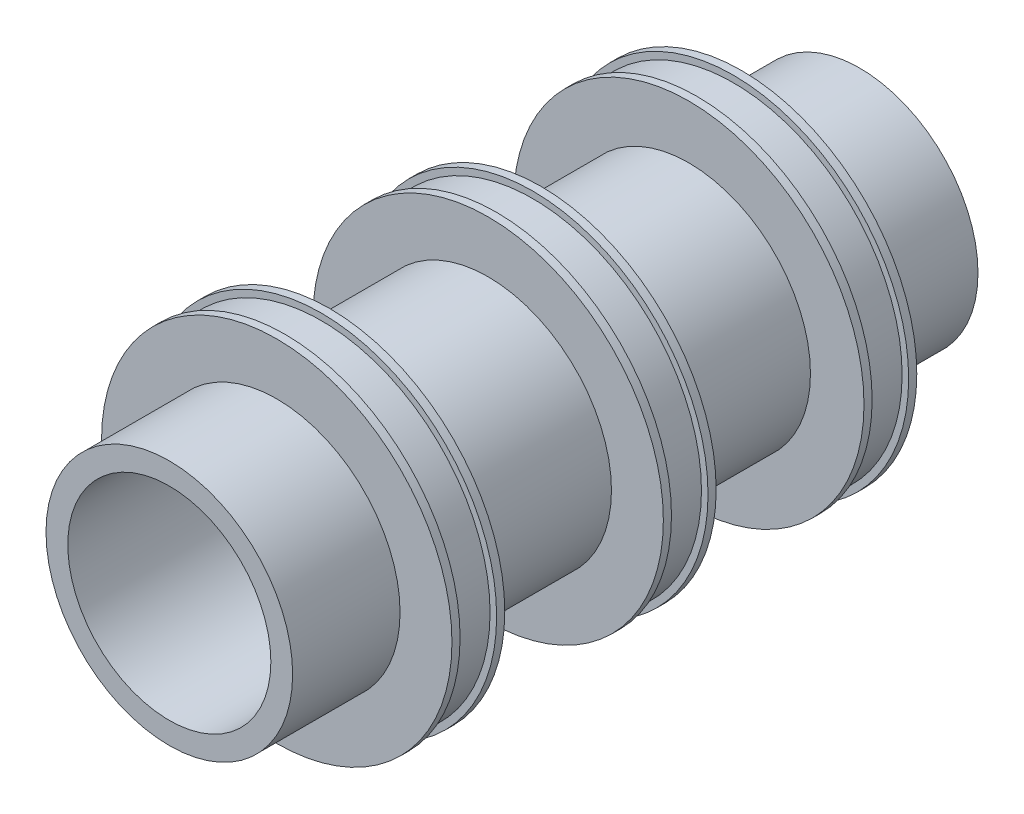
SolidWorks part; units mm, degrees
ref_plane "Front Plane" through (0, 0, 0) normal (0, 0, 1) x (1, 0, 0)
ref_plane "Top Plane" through (0, 0, 0) normal (0, 1, 0) x (1, 0, 0)
ref_plane "Right Plane" through (0, 0, 0) normal (1, 0, 0) x (0, 0, -1)
sketch "Sketch1" plane through (0, 0, 0) normal (1, 0, 0) x (0, 0, -1)
  line L0 (-119.0608, 0) -> (108.9248, 0) construction
  line L1 (-119.0608, 25) -> (108.9248, 25) construction
  line L30 (-85, 25) -> (85, 25)
  line L31 (-85, 25) -> (-85, 30.3639)
  line L32 (-85, 30.3639) -> (-58.5522, 30.3639)
  line L33 (-58.5522, 30.3639) -> (-58.5522, 43.1442)
  line L34 (-58.5522, 43.1442) -> (-56.5522, 43.1442)
  line L35 (-56.5522, 43.1442) -> (-56.5522, 41.53)
  line L36 (-56.5522, 41.53) -> (-47.5522, 41.53)
  line L37 (-47.5522, 41.53) -> (-47.5522, 43.1442)
  line L38 (-47.5522, 43.1442) -> (-45.5522, 43.1442)
  line L39 (-45.5522, 43.1442) -> (-45.5522, 30.3639)
  line L40 (-45.5522, 30.3639) -> (-6.5, 30.3639)
  line L41 (-6.5, 30.3639) -> (-6.5, 43.1442)
  line L42 (-6.5, 43.1442) -> (-4.5, 43.1442)
  line L43 (-4.5, 43.1442) -> (-4.5, 41.53)
  line L44 (-4.5, 41.53) -> (4.5, 41.53)
  line L45 (4.5, 41.53) -> (4.5, 43.1442)
  line L46 (4.5, 43.1442) -> (6.5, 43.1442)
  line L47 (6.5, 43.1442) -> (6.5, 29.9619)
  line L48 (6.5, 29.9619) -> (42.9013, 29.9619)
  line L49 (42.9013, 29.9619) -> (42.9013, 43.1442)
  line L50 (42.9013, 43.1442) -> (44.9013, 43.1442)
  line L51 (44.9013, 43.1442) -> (44.9013, 41.53)
  line L52 (44.9013, 41.53) -> (53.9013, 41.53)
  line L53 (53.9013, 41.53) -> (53.9013, 43.1442)
  line L54 (53.9013, 43.1442) -> (55.9013, 43.1442)
  line L55 (55.9013, 43.1442) -> (55.9013, 29.1152)
  line L56 (55.9013, 29.1152) -> (85, 29.1152)
  line L57 (85, 29.1152) -> (85, 25)
  point P7 (0, 25)
  point P18 (0, 41.53)
  dimension "D1" = 25
  dimension "D2" = 170
  dimension "D3" = 9
  dimension "D4" = 2
  dimension "D5" = 2
  dimension "D6" = 9
  dimension "D7" = 2
  dimension "D8" = 2
  dimension "D9" = 9
  dimension "D10" = 2
  dimension "D11" = 2
  dimension "D12" = 26.4478
  dimension "D13" = 58.2304
revolve "Revolve2" add sketch "Sketch1" angle 360 about L0
